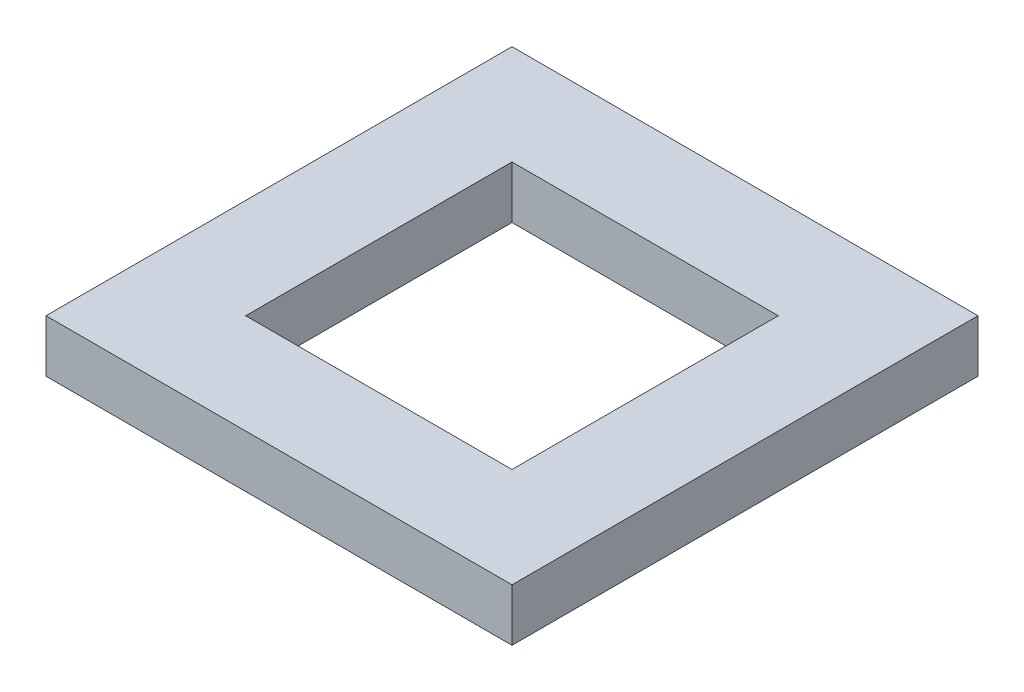
SolidWorks part; units mm, degrees
ref_plane "Front Plane" through (0, 0, 0) normal (0, 0, 1) x (1, 0, 0)
ref_plane "Top Plane" through (0, 0, 0) normal (0, 1, 0) x (1, 0, 0)
ref_plane "Right Plane" through (0, 0, 0) normal (1, 0, 0) x (0, 0, -1)
sketch "Sketch1" plane through (0, 0, 0) normal (0, 1, 0) x (1, 0, 0)
  line L0 (50.8, -50.8) -> (50.8, 50.8) construction
  line L1 (44.45, 44.45) -> (-44.45, 44.45)
  line L2 (44.45, 44.45) -> (44.45, -44.45)
  line L3 (44.45, -44.45) -> (-44.45, -44.45)
  line L4 (-44.45, 44.45) -> (-44.45, -44.45)
  line L5 (44.45, 44.45) -> (-44.45, -44.45) construction
  line L6 (44.45, -44.45) -> (-44.45, 44.45) construction
  line L7 (-50.8, -50.8) -> (50.8, -50.8) construction
  point P0 (0, 0)
  dimension "D1" = 6.35
  dimension "D2" = 6.35
extrude "Boss-Extrude1" add sketch "Sketch1" along normal blind 10
sketch "Sketch2" plane through (0, 10, 0) normal (0, 1, 0) x (1, 0, 0)
  line L4 (25.4, 25.4) -> (-25.4, 25.4)
  line L5 (-25.4, 25.4) -> (-25.4, -25.4)
  line L6 (-25.4, -25.4) -> (25.4, -25.4)
  line L7 (25.4, -25.4) -> (25.4, 25.4)
  line L8 (25.4, 25.4) -> (-25.4, 25.4)
  line L9 (-25.4, 25.4) -> (-25.4, -25.4)
  line L10 (-25.4, -25.4) -> (25.4, -25.4)
  line L11 (25.4, -25.4) -> (25.4, 25.4)
  dimension "D1" = 0
extrude "Cut-Extrude1" cut sketch "Sketch2" against normal up to next
